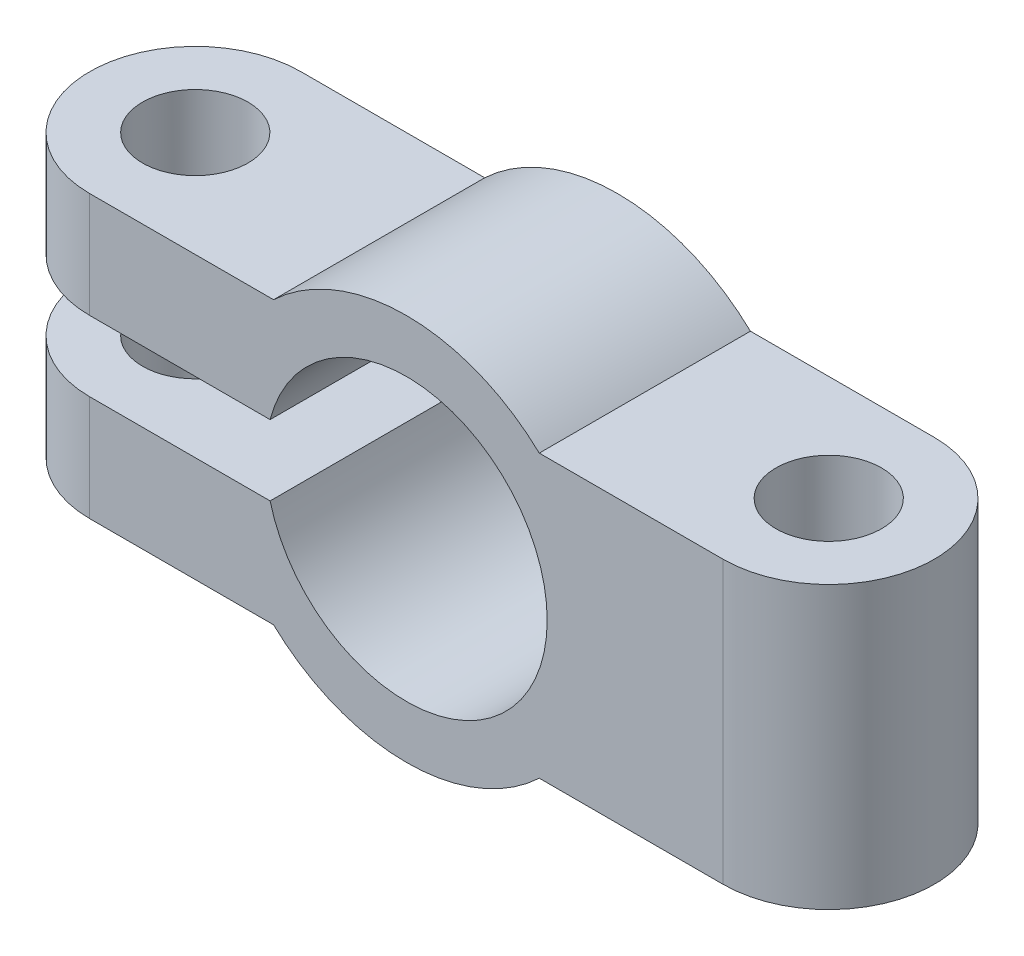
SolidWorks part; units mm, degrees
ref_plane "前视基准面" through (0, 0, 0) normal (0, 0, 1) x (1, 0, 0)
ref_plane "上视基准面" through (0, 0, 0) normal (0, 1, 0) x (1, 0, 0)
ref_plane "右视基准面" through (0, 0, 0) normal (1, 0, 0) x (0, 0, -1)
sketch "草图1" plane through (0, 0, 0) normal (0, 0, 1) x (1, 0, 0)
  line L0 (-15.855, 0) -> (12, 0) construction
  line L1 (12, 4) -> (12, -4)
  line L2 (12, -4) -> (3.7749, -4)
  line L3 (-12, -4) -> (-3.7749, -4)
  line L4 (-12, -4) -> (-12, -1)
  line L5 (-12, -1) -> (-3.873, -1)
  line L6 (-12, 1) -> (-3.873, 1)
  line L7 (-12, 1) -> (-12, 4)
  line L8 (-12, 4) -> (-3.7749, 4)
  line L9 (12, 4) -> (3.7749, 4)
  arc A0 (-3.873, -1) -> (-3.873, 1) centre (0, 0) ccw
  arc A1 (-3.7749, -4) -> (3.7749, -4) centre (0, 0) ccw
  arc A2 (3.7749, 4) -> (-3.7749, 4) centre (0, 0) ccw
  dimension "D2" = 8
  dimension "D3" = 11
  dimension "D1" = 8
  dimension "D4" = 12
  dimension "D5" = 3
  dimension "D6" = 3
  dimension "D7" = 1
  dimension "D8" = 24
extrude "凸台-拉伸1" add sketch "草图1" along normal blind 6
sketch "草图2" plane through (0, -4, 0) normal (0, -1, 0) x (1, 0, 0)
  line L0 (-12, 6) -> (-3.7749, 6) construction
  line L1 (-12, 6) -> (-12, 0) construction
  line L2 (-12, 0) -> (-3.7749, 0) construction
  line L3 (-12, 6) -> (-9, 6)
  line L4 (-12, 6) -> (-12, 0)
  line L5 (-12, 0) -> (-3.7749, 0)
  line L6 (3.7749, 6) -> (12, 6) construction
  line L7 (12, 6) -> (12, 0) construction
  line L8 (3.7749, 0) -> (12, 0) construction
  line L9 (9, 6) -> (12, 6)
  line L10 (12, 6) -> (12, 0)
  line L11 (9, 0) -> (12, 0)
  arc A0 (-9, 6) -> (-9, 0) centre (-9, 3) ccw
  arc A1 (9, 0) -> (9, 6) centre (9, 3) ccw
  line M1 (-12, 0) -> (-3.7749, 0)
  line M3 (-3.7749, 6) -> (-12, 6)
  line M4 (-12, 6) -> (-12, 0)
extrude "切除-拉伸1" cut sketch "草图2" against normal through all contours A0 L4 M1 | A0 M3 M4 | A1 L11 L10 | A1 L10 L9
sketch "草图3" plane through (0, -4, 0) normal (0, -1, 0) x (1, 0, 0)
  circle A0 centre (-9, 3) radius 1.5
  circle A1 centre (9, 3) radius 1.5
  dimension "D1" = 3
  dimension "D2" = 3
extrude "切除-拉伸2" cut sketch "草图3" against normal through all
